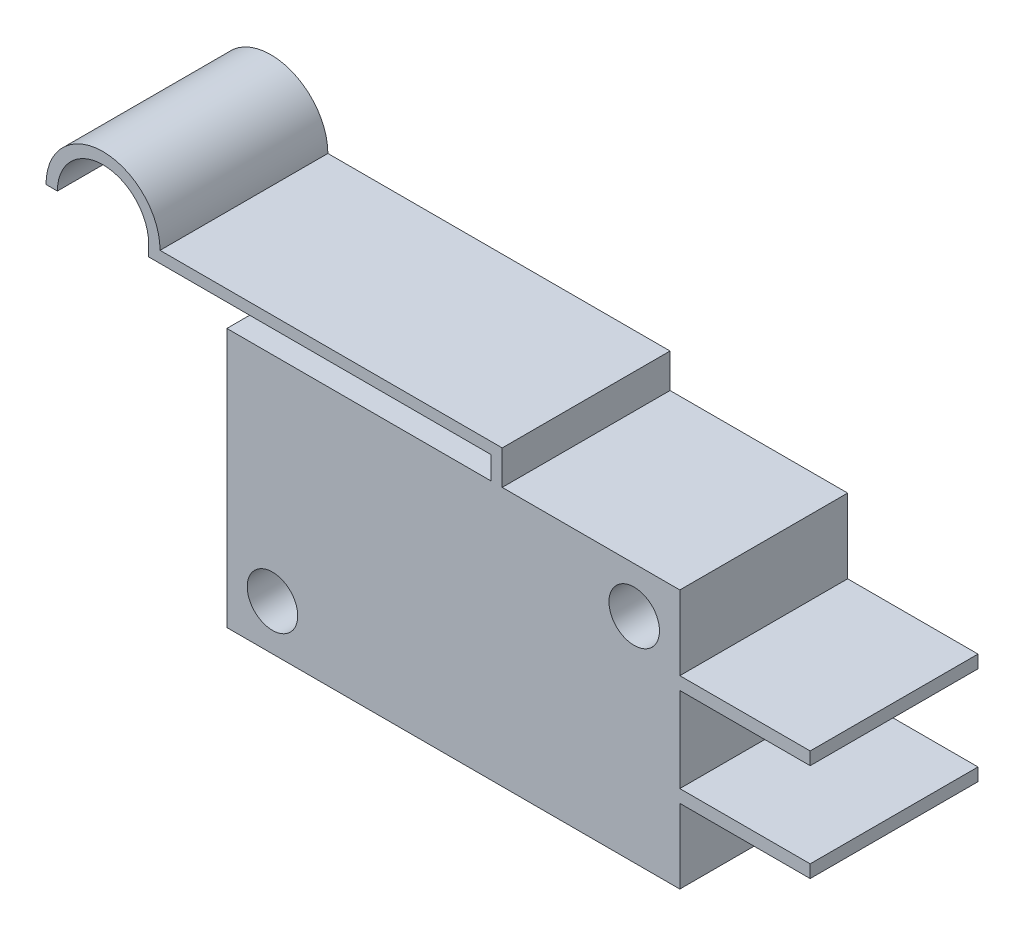
SolidWorks part; units mm, degrees
ref_plane "前视基准面" through (0, 0, 0) normal (0, 0, 1) x (1, 0, 0)
ref_plane "上视基准面" through (0, 0, 0) normal (0, 1, 0) x (1, 0, 0)
ref_plane "右视基准面" through (0, 0, 0) normal (1, 0, 0) x (0, 0, -1)
sketch "草图3" plane through (0, 0, 0) normal (0, 0, 1) x (1, 0, 0)
  line L1 (0, 0) -> (-27.8, 0)
  line L2 (0, 0) -> (0, 15.9)
  line L3 (0, 15.9) -> (-27.8, 15.9)
  line L4 (-27.8, 0) -> (-27.8, 15.9)
  dimension "D1" = 15.9
  dimension "D2" = 27.8
extrude "凸台-拉伸1" add sketch "草图3" along normal blind 10.3
sketch "草图4" plane through (0, 0, 10.3) normal (0, 0, 1) x (1, 0, 0)
  line L0 (-27.8, 7.95) -> (3.1684, 7.95) construction
  line L1 (-27.8, 15.9) -> (-27.8, 0) construction
  line L2 (-13.9, 15.9) -> (-13.9, 7.95) construction
  line L3 (0, 15.9) -> (-27.8, 15.9) construction
  circle A0 centre (-2.8, 13.1) radius 1.55
  circle A1 centre (-25, 2.8) radius 1.55
  dimension "D1" = 3.1
  dimension "D2" = 3.1
  dimension "D3" = 5.15
  dimension "D4" = 5.15
  dimension "D5" = 11.1
  dimension "D6" = 11.1
extrude "切除-拉伸1" cut sketch "草图4" against normal blind 10.3
sketch "草图5" plane through (0, 0, 10.3) normal (0, 0, 1) x (1, 0, 0)
  line L0 (0, 0) -> (0, 15.9) construction
  line L1 (0, 10.5575) -> (8, 10.5575)
  line L2 (0, 10.5575) -> (0, 11.3425)
  line L3 (0, 11.3425) -> (8, 11.3425)
  line L4 (8, 10.5575) -> (8, 11.3425)
  line L5 (0, 7.95) -> (11.8923, 7.95) construction
  line L6 (0, 5.3425) -> (0, 4.5575)
  line L7 (0, 5.3425) -> (8, 5.3425)
  line L8 (8, 5.3425) -> (8, 4.5575)
  line L9 (0, 4.5575) -> (8, 4.5575)
  line L10 (0, 10.95) -> (8, 10.95) construction
  line L11 (0, 4.95) -> (8, 4.95) construction
  dimension "D1" = 6
  dimension "D2" = 8
extrude "凸台-拉伸2" add sketch "草图5" against normal blind 10.3
sketch "草图6" plane through (0, 0, 10.3) normal (0, 0, 1) x (1, 0, 0)
  line L0 (0, 15.9) -> (-27.8, 15.9) construction
  line L1 (-31.9, 18) -> (-22.4525, 18)
  line L3 (-31.8963, 17.3) -> (-11.6, 17.3)
  line L5 (-22.4525, 18) -> (-10.9, 18)
  line L6 (-11.6, 17.3) -> (-11.6, 15.9)
  line L7 (-11.6, 15.9) -> (-10.9, 15.9)
  line L8 (-10.9, 18) -> (-10.9, 15.9)
  line L9 (-32.6, 18) -> (-32.6, 17.3)
  line L10 (-32.6, 17.3) -> (-31.8963, 17.3)
  line L12 (-38.9, 18) -> (-38.2, 18)
  arc A0 (-31.9, 18) -> (-38.9, 18) centre (-35.4, 18) ccw
  arc A1 (-32.6, 18) -> (-38.2, 18) centre (-35.4, 18) ccw
  circle A2 centre (-2.8, 13.1) radius 1.55 construction
  circle A3 centre (-25, 2.8) radius 1.55 construction
  point P16 (-35.4, 20.8)
  dimension "D6" = 3.5
  dimension "D7" = 15.2
  dimension "D1" = 0.7
  dimension "D2" = 0.7
  dimension "D3" = 0.7
  dimension "D4" = 8.1
  dimension "D5" = 32.6
extrude "凸台-拉伸3" add sketch "草图6" against normal blind 10.3
